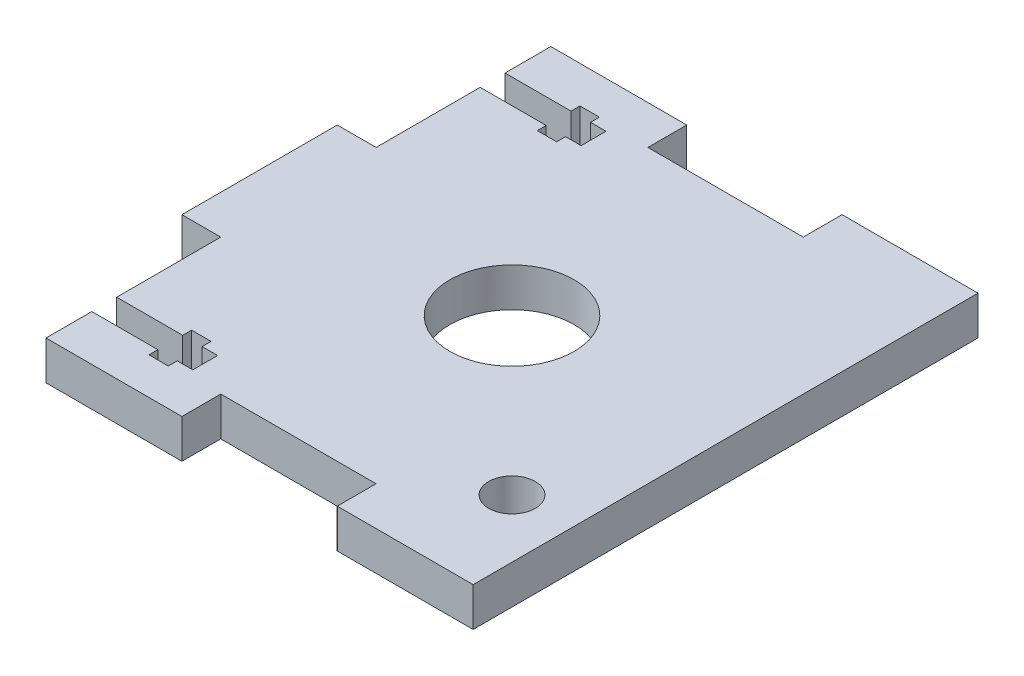
SolidWorks part; units mm, degrees
ref_plane "Plan de face" through (0, 0, 0) normal (0, 0, 1) x (1, 0, 0)
ref_plane "Plan de dessus" through (0, 0, 0) normal (0, 1, 0) x (1, 0, 0)
ref_plane "Plan de droite" through (0, 0, 0) normal (1, 0, 0) x (0, 0, -1)
sketch "Esquisse1" plane through (0, 0, 0) normal (0, 1, 0) x (1, 0, 0)
  line L1 (17.5, -5) -> (37.5, -5)
  line L3 (17.5, -60) -> (37.5, -60)
  line L5 (0, 0) -> (17.5, 0)
  line L6 (17.5, 0) -> (17.5, -5)
  line L7 (37.5, -5) -> (37.5, 0)
  line L8 (37.5, 0) -> (55, 0)
  line L10 (55, -32.5) -> (31.3794, -32.5) construction
  line L11 (55, 0) -> (55, -60)
  line L12 (0, 0) -> (0, -22.5)
  line L13 (0, -60) -> (0, -65)
  line L14 (0, -65) -> (17.5, -65)
  line L15 (17.5, -65) -> (17.5, -60)
  line L16 (55, -60) -> (55, -65)
  line L17 (55, -65) -> (37.5, -65)
  line L18 (37.5, -65) -> (37.5, -60)
  line L19 (27.5, -5) -> (27.5, -47.0906) construction
  line L20 (0, -22.5) -> (-5, -22.5)
  line L21 (-5, -22.5) -> (-5, -42.5)
  line L22 (-5, -42.5) -> (0, -42.5)
  line L23 (0, -42.5) -> (0, -60)
  dimension "D2" = 55
  dimension "D3" = 20
  dimension "D5" = 5
  dimension "D1" = 55
  dimension "D6" = 5
  dimension "D4" = 27.5
  dimension "D7" = 20
  dimension "D9" = 5
  dimension "D8" = 27.5
  dimension "D10" = 10
extrude "Boss.-Extru.1" add sketch "Esquisse1" along normal blind 5
sketch "Esquisse2" plane through (0, 5, 0) normal (0, 1, 0) x (1, 0, 0)
  line L0 (27.5, -5) -> (27.5, -60) construction
  line L1 (37.5, -5) -> (17.5, -5) construction
  line L2 (17.5, -60) -> (37.5, -60) construction
  line L3 (-5, -32.5) -> (55, -32.5) construction
  line L4 (-5, -22.5) -> (-5, -42.5) construction
  line L5 (55, -65) -> (55, 0) construction
  circle A0 centre (27.5, -32.5) radius 8
  point P14 (27.5, -32.5)
  dimension "D1" = 16
extrude "Enlèv. mat.-Extru.1" cut sketch "Esquisse2" against normal blind 10
sketch "Esquisse3" plane through (0, 5, 0) normal (0, 1, 0) x (1, 0, 0)
  line L0 (0, 0) -> (0, -22.5) construction
  line L1 (13, -5.9) -> (11, -5.9)
  line L2 (13, -5.9) -> (13, -9.1)
  line L3 (13, -9.1) -> (11, -9.1)
  line L4 (0, -5.9) -> (0, -9.1)
  line L5 (-5, -32.5) -> (6.7554, -32.5) construction
  line L7 (13, -7.5) -> (0, -7.5) construction
  line L8 (11, -5.9) -> (11, -4.75)
  line L9 (11, -4.75) -> (8.5, -4.75)
  line L10 (8.5, -4.75) -> (8.5, -5.9)
  line L11 (8.5, -5.9) -> (0, -5.9)
  line L12 (11, -9.1) -> (11, -10.25)
  line L13 (11, -10.25) -> (8.5, -10.25)
  line L14 (8.5, -10.25) -> (8.5, -9.1)
  line L15 (8.5, -9.1) -> (0, -9.1)
  line L17 (-5, -22.5) -> (-5, -42.5) construction
  point P17 (9.75, -10.25)
  point P19 (11, -9.675)
  dimension "D1" = 25
  dimension "D2" = 3.2
  dimension "D3" = 13
  dimension "D4" = 5.5
  dimension "D5" = 2.75
  dimension "D6" = 2.5
  dimension "D7" = 2
extrude "Enlèv. mat.-Extru.2" cut sketch "Esquisse3" against normal blind 10
ref_plane "Plan1" through (0, 0, 32.5) normal (0, 0, -1) x (-1, 0, 0)
mirror "Symétrie1" about plane through (0, 0, 32.5) normal (0, 0, -1) of "Enlèv. mat.-Extru.2"
sketch "Esquisse4" plane through (0, 5, 0) normal (0, 1, 0) x (1, 0, 0)
  line L0 (2.75, -32.5) -> (-2.75, -32.5) construction
  circle A0 centre (47.5, -52.5) radius 3
  circle A1 centre (27.5, -32.5) radius 8 construction
  dimension "D2" = 6
  dimension "D1" = 20
  dimension "D3" = 20
extrude "Enlèv. mat.-Extru.3" cut sketch "Esquisse4" against normal blind 10
equation "\"D6@Esquisse1\"=\"D5@Esquisse1\""
equation "\"D4@Esquisse1\"=\"D2@Esquisse1\"/2"
equation "\"D9@Esquisse1\"=\"D5@Esquisse1\""
equation "\"D8@Esquisse1\"=\"D1@Esquisse1\"/2"
equation "\"D10@Esquisse1\"=\"D7@Esquisse1\"/2"
